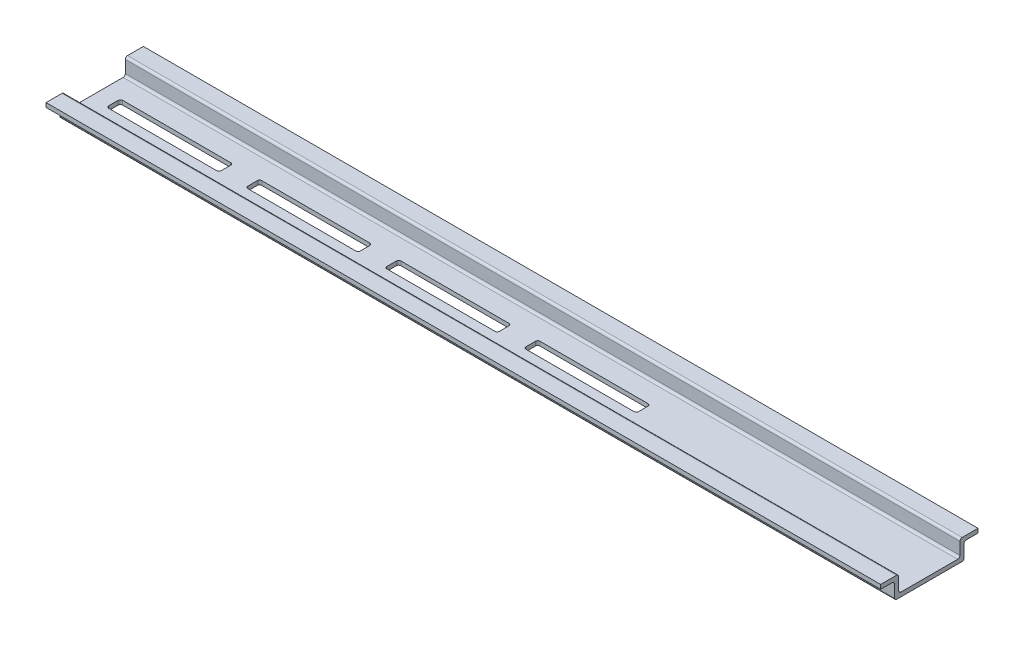
SolidWorks part; units mm, degrees
ref_plane "Спереди" through (0, 0, 0) normal (0, 0, 1) x (1, 0, 0)
ref_plane "Сверху" through (0, 0, 0) normal (0, 1, 0) x (1, 0, 0)
ref_plane "Справа" through (0, 0, 0) normal (1, 0, 0) x (0, 0, -1)
sketch "Эскиз1" plane through (0, 0, 0) normal (1, 0, 0) x (0, 0, -1)
  line L0 (0, 7.5241) -> (0, 6)
  line L1 (0, 6) -> (4.2, 6)
  line L2 (5, 5.2) -> (5, 0.8)
  line L3 (5.8, 0) -> (29.2, 0)
  line L4 (30, 0.8) -> (30, 5.2)
  line L5 (30.8, 6) -> (35, 6)
  line L6 (35, 6) -> (35, 7.5)
  line L7 (35, 7.5) -> (29.3, 7.5)
  line L8 (28.5, 6.7) -> (28.5, 2.3)
  line L9 (27.7, 1.5) -> (7.3, 1.5)
  line L10 (6.5, 2.3) -> (6.5, 6.7241)
  line L11 (5.7, 7.5241) -> (0, 7.5241)
  arc A0 (4.2, 6) -> (5, 5.2) centre (4.2, 5.2) cw
  arc A1 (7.3, 1.5) -> (6.5, 2.3) centre (7.3, 2.3) cw
  arc A2 (5, 0.8) -> (5.8, 0) centre (5.8, 0.8) ccw
  arc A3 (29.2, 0) -> (30, 0.8) centre (29.2, 0.8) ccw
  arc A4 (28.5, 2.3) -> (27.7, 1.5) centre (27.7, 2.3) cw
  arc A5 (30, 5.2) -> (30.8, 6) centre (30.8, 5.2) cw
  arc A6 (29.3, 7.5) -> (28.5, 6.7) centre (29.3, 6.7) ccw
  arc A7 (6.5, 6.7241) -> (5.7, 7.5241) centre (5.7, 6.7241) ccw
  point P17 (6.5, 1.5)
  point P24 (28.5, 1.5)
  dimension "D1" = 0.8
extrude "Бобышка-Вытянуть1" add sketch "Эскиз1" along normal blind 300
sketch "Эскиз2" plane through (0, 1.5, 0) normal (0, 1, 0) x (1, 0, 0)
  line L0 (57.0508, 20.5) -> (95.8734, 20.5)
  line L1 (7.0508, 20.5) -> (45.8734, 20.5)
  line L2 (6.2508, 19.7) -> (6.2508, 16.3)
  line L3 (7.0508, 15.5) -> (45.8734, 15.5)
  line L4 (46.6734, 19.7) -> (46.6734, 16.3)
  line L5 (57.0508, 15.5) -> (95.8734, 15.5)
  line L6 (96.6734, 19.7) -> (96.6734, 16.3)
  line L7 (56.2508, 19.7) -> (56.2508, 16.3)
  line L8 (107.0508, 20.5) -> (145.8734, 20.5)
  line L9 (107.0508, 15.5) -> (145.8734, 15.5)
  line L10 (146.6734, 19.7) -> (146.6734, 16.3)
  line L11 (106.2508, 19.7) -> (106.2508, 16.3)
  line L12 (157.0508, 20.5) -> (195.8734, 20.5)
  line L13 (157.0508, 15.5) -> (195.8734, 15.5)
  line L14 (196.6734, 19.7) -> (196.6734, 16.3)
  line L15 (156.2508, 19.7) -> (156.2508, 16.3)
  arc A0 (45.8734, 15.5) -> (46.6734, 16.3) centre (45.8734, 16.3) ccw
  arc A1 (45.8734, 20.5) -> (46.6734, 19.7) centre (45.8734, 19.7) cw
  arc A2 (7.0508, 20.5) -> (6.2508, 19.7) centre (7.0508, 19.7) ccw
  arc A3 (6.2508, 16.3) -> (7.0508, 15.5) centre (7.0508, 16.3) ccw
  arc A4 (95.8734, 15.5) -> (96.6734, 16.3) centre (95.8734, 16.3) ccw
  arc A5 (95.8734, 20.5) -> (96.6734, 19.7) centre (95.8734, 19.7) cw
  arc A6 (57.0508, 20.5) -> (56.2508, 19.7) centre (57.0508, 19.7) ccw
  arc A7 (56.2508, 16.3) -> (57.0508, 15.5) centre (57.0508, 16.3) ccw
  arc A8 (145.8734, 15.5) -> (146.6734, 16.3) centre (145.8734, 16.3) ccw
  arc A9 (145.8734, 20.5) -> (146.6734, 19.7) centre (145.8734, 19.7) cw
  arc A10 (107.0508, 20.5) -> (106.2508, 19.7) centre (107.0508, 19.7) ccw
  arc A11 (106.2508, 16.3) -> (107.0508, 15.5) centre (107.0508, 16.3) ccw
  arc A12 (195.8734, 15.5) -> (196.6734, 16.3) centre (195.8734, 16.3) ccw
  arc A13 (195.8734, 20.5) -> (196.6734, 19.7) centre (195.8734, 19.7) cw
  arc A14 (157.0508, 20.5) -> (156.2508, 19.7) centre (157.0508, 19.7) ccw
  arc A15 (156.2508, 16.3) -> (157.0508, 15.5) centre (157.0508, 16.3) ccw
  dimension "D1" = 0.8
  dimension "D2" = 4
extrude "Вырез-Вытянуть1" cut sketch "Эскиз2" against normal blind 10
